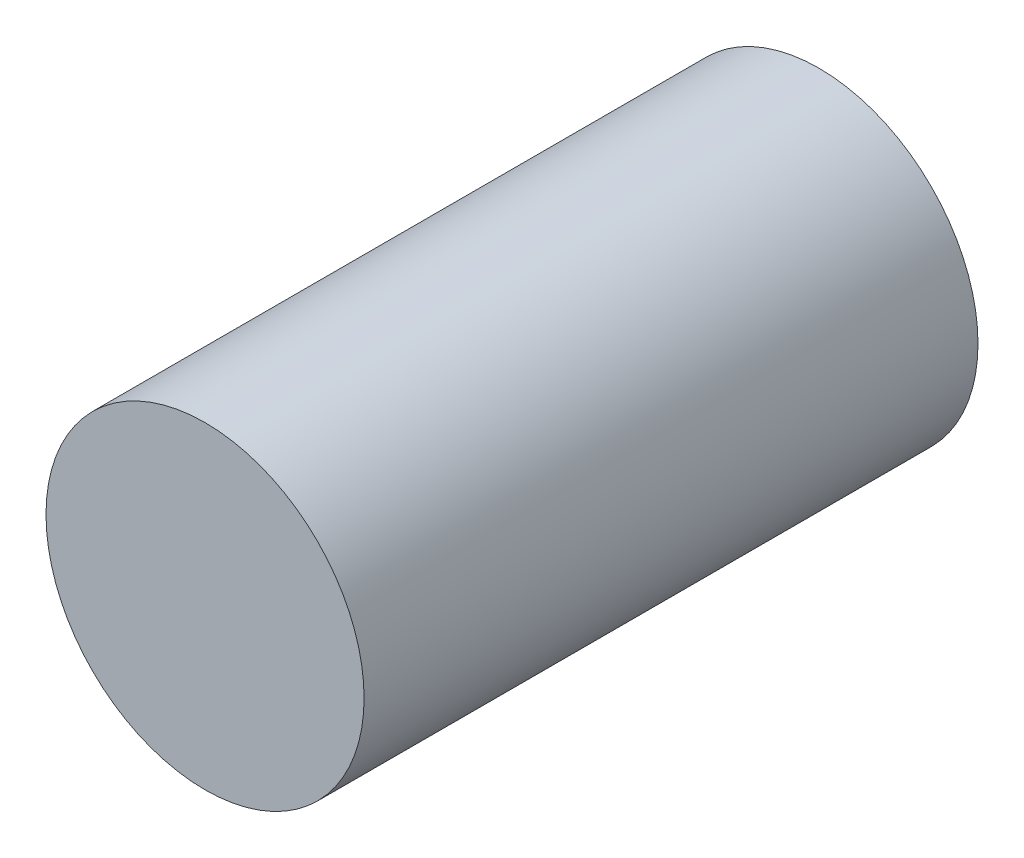
SolidWorks part; units mm, degrees
ref_plane "Front Plane" through (0, 0, 0) normal (0, 0, 1) x (1, 0, 0)
ref_plane "Top Plane" through (0, 0, 0) normal (0, 1, 0) x (1, 0, 0)
ref_plane "Right Plane" through (0, 0, 0) normal (1, 0, 0) x (0, 0, -1)
sketch "Sketch1" plane through (0, 0, 0) normal (0, 0, 1) x (1, 0, 0)
  circle A0 centre (0, 0) radius 1
  dimension "D1" = 2
extrude "Boss-Extrude1" add sketch "Sketch1" along normal mid plane 3.86
